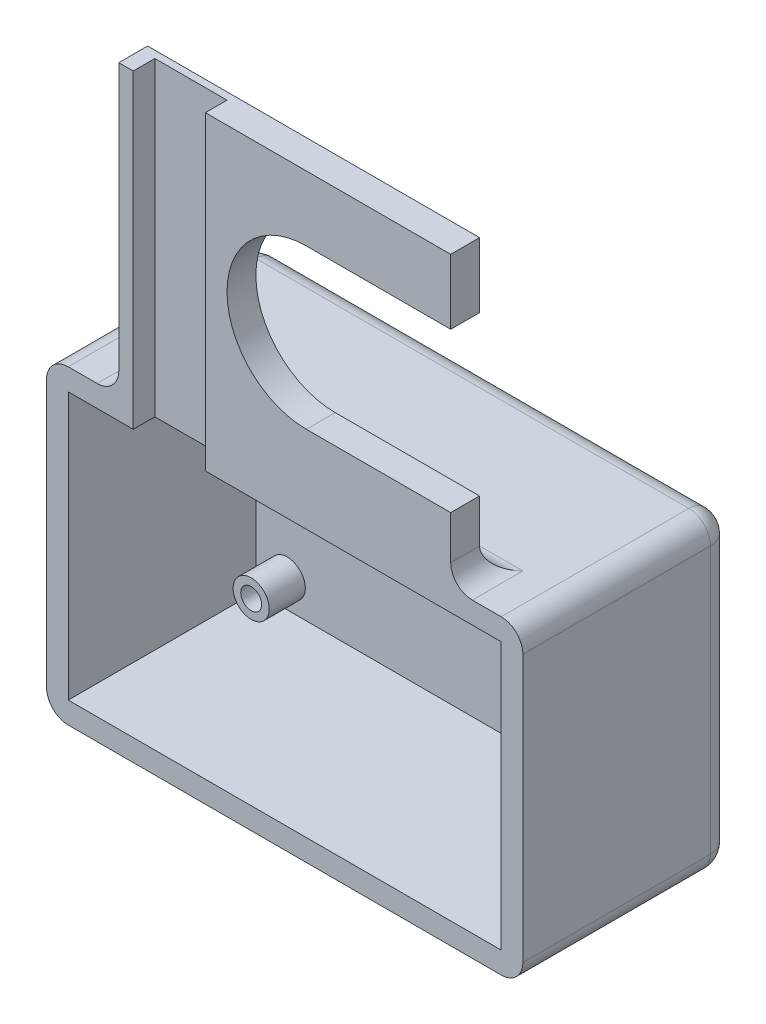
SolidWorks part; units mm, degrees
ref_plane "前视基准面" through (0, 0, 0) normal (0, 0, 1) x (1, 0, 0)
ref_plane "上视基准面" through (0, 0, 0) normal (0, 1, 0) x (1, 0, 0)
ref_plane "右视基准面" through (0, 0, 0) normal (1, 0, 0) x (0, 0, -1)
sketch "草图1" plane through (0, 0, 0) normal (0, 0, 1) x (1, 0, 0)
  line L0 (-30.8371, -4.1792) -> (29.1629, -4.1792) construction
  line L1 (32.1629, 17.3208) -> (-33.8371, 17.3208)
  line L2 (32.1629, 17.3208) -> (32.1629, -25.6792)
  line L3 (32.1629, -25.6792) -> (-33.8371, -25.6792)
  line L4 (-33.8371, 17.3208) -> (-33.8371, -25.6792)
  line L5 (-30.8371, 14.3208) -> (29.1629, 14.3208)
  line L6 (-30.8371, 14.3208) -> (-30.8371, -22.6792)
  line L7 (-30.8371, -22.6792) -> (29.1629, -22.6792)
  line L8 (29.1629, 14.3208) -> (29.1629, -22.6792)
  line L9 (-0.8371, 17.3208) -> (-0.8371, -25.6792) construction
  point P12 (-0.8371, -4.1792)
  point P13 (-0.8371, -4.1792)
  dimension "D1" = 66
  dimension "D2" = 60
  dimension "D3" = 43
  dimension "D4" = 37
extrude "凸台-拉伸1" add sketch "草图1" along normal blind 26
sketch "草图2" plane through (0, 0, 0) normal (0, 0, -1) x (-1, 0, 0)
  line L1 (-32.1629, 17.3208) -> (33.8371, 17.3208)
  line L2 (-32.1629, 17.3208) -> (-32.1629, -25.6792)
  line L3 (-32.1629, -25.6792) -> (33.8371, -25.6792)
  line L4 (33.8371, 17.3208) -> (33.8371, -25.6792)
extrude "凸台-拉伸2" add sketch "草图2" along normal blind 3
sketch "草图3" plane through (0, 17.3208, 0) normal (0, 1, 0) x (1, 0, 0)
  line L0 (32.1629, -26) -> (-33.8371, -26) construction
  line L1 (-21.8371, -23) -> (-11.8371, -23)
  line L2 (-21.8371, -23) -> (-21.8371, -26)
  line L3 (-21.8371, -26) -> (-11.8371, -26)
  line L4 (-11.8371, -23) -> (-11.8371, -26)
  line L5 (-21.8371, -24.5) -> (-11.8371, -24.5) construction
  line L8 (-33.8371, -26) -> (-33.8371, 3) construction
  line L9 (-23.8371, -22) -> (22.1629, -22)
  line L10 (-23.8371, -22) -> (-23.8371, -26)
  line L18 (32.1629, -26) -> (32.1629, 3) construction
  line L19 (22.1629, -22) -> (22.1629, -26)
  line L20 (22.1629, -26) -> (-11.8371, -26)
  line L21 (-21.8371, -26) -> (-23.8371, -26)
  point P14 (-20.6739, -23)
  point P17 (-24.7864, -11.1522)
  point P18 (-26.6127, -11.4341)
  dimension "D1" = 3
  dimension "D2" = 10
  dimension "D3" = 10
  dimension "D4" = 4
  dimension "D5" = 10
  dimension "D6" = 2
extrude "凸台-拉伸3" add sketch "草图3" along normal blind 40
sketch "草图4" plane through (0, 17.3208, 0) normal (0, 1, 0) x (1, 0, 0)
  line L1 (-21.8371, -23) -> (-11.8371, -23)
  line L2 (-21.8371, -23) -> (-21.8371, -26)
  line L3 (-21.8371, -26) -> (-11.8371, -26)
  line L4 (-11.8371, -23) -> (-11.8371, -26)
extrude "切除-拉伸1" cut sketch "草图4" against normal up to next
sketch "草图6" plane through (0, 0, 0) normal (0, 0, 1) x (1, 0, 0)
  line L0 (-30.8371, -4.1792) -> (29.1629, -4.1792) construction
  line L1 (-30.8371, 14.3208) -> (-30.8371, -22.6792) construction
  line L2 (29.1629, -22.6792) -> (29.1629, 14.3208) construction
  line L3 (-0.8371, -22.6792) -> (-0.8371, 14.3208) construction
  line L4 (-30.8371, -22.6792) -> (29.1629, -22.6792) construction
  line L5 (29.1629, 14.3208) -> (-30.8371, 14.3208) construction
  circle A0 centre (24.8129, -18.8292) radius 1.45
  circle A1 centre (24.8129, -18.8292) radius 2.5
  circle A2 centre (-26.4871, -18.8292) radius 1.45
  circle A3 centre (-26.4871, -18.8292) radius 2.5
  circle A4 centre (24.8129, 10.4708) radius 1.45
  circle A5 centre (24.8129, 10.4708) radius 2.5
  circle A6 centre (-26.4871, 10.4708) radius 1.45
  circle A7 centre (-26.4871, 10.4708) radius 2.5
  dimension "D3" = 2.9
  dimension "D1" = 14.65
  dimension "D2" = 25.65
extrude "凸台-拉伸5" add sketch "草图6" along normal blind 5
sketch "草图10" plane through (0, 0, 26) normal (0, 0, 1) x (1, 0, 0)
  line L0 (22.1629, 37.3208) -> (-11.8371, 37.3208) construction
  line L1 (22.1629, 57.3208) -> (22.1629, 17.3208) construction
  line L2 (-11.8371, 57.3208) -> (-11.8371, 14.3208) construction
  line L3 (2.1629, 26.3208) -> (22.1629, 26.3208)
  line L4 (22.1629, 26.3208) -> (22.1629, 48.3208)
  line L5 (2.1629, 48.3208) -> (22.1629, 48.3208)
  arc A0 (2.1629, 48.3208) -> (2.1629, 26.3208) centre (2.1629, 37.3208) ccw
  point P13 (0, 0)
  dimension "D2" = 22
  dimension "D1" = 14
extrude "切除-拉伸2" cut sketch "草图10" against normal up to next
fillet "圆角1" radius 3 8 edges at (32.1629, 17.3208, 11.5) (32.1629, -4.1792, -3) (32.1629, -25.6792, 11.5) (-0.8371, -25.6792, -3) (-33.8371, -25.6792, 11.5) (-33.8371, 17.3208, 11.5) (-33.8371, -4.1792, -3) (-0.8371, 17.3208, -3)
fillet "圆角2" radius 3 3 edges at (22.1629, 17.3208, 24) (-23.8371, 17.3208, 24) (-0.8371, 17.3208, 22)
